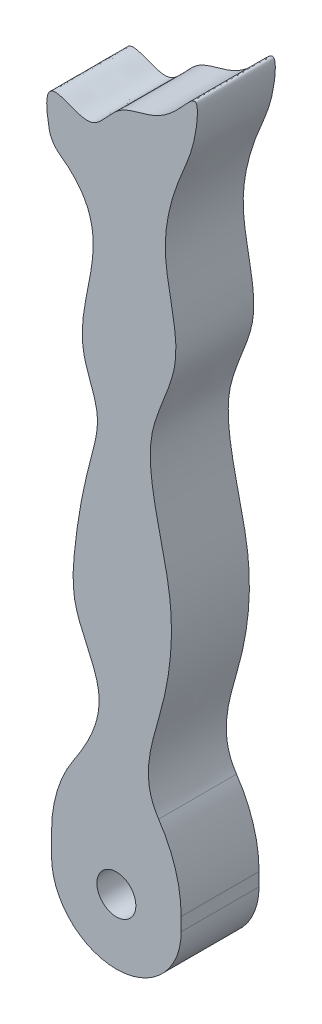
SolidWorks part; units mm, degrees
ref_plane "Front Plane" through (0, 0, 0) normal (0, 0, 1) x (1, 0, 0)
ref_plane "Top Plane" through (0, 0, 0) normal (0, 1, 0) x (1, 0, 0)
ref_plane "Right Plane" through (0, 0, 0) normal (1, 0, 0) x (0, 0, -1)
sketch "Sketch1" plane through (0, 0, 0) normal (0, 0, 1) x (1, 0, 0)
  line L0 (4.99, 0) -> (4.99, -9.98) construction
  line L1 (0, 0) -> (9.98, 0)
  line L2 (0, 0) -> (0, -9.98)
  line L3 (0, -9.98) -> (9.98, -9.98)
  line L4 (9.98, 0) -> (9.98, -9.98)
  line L5 (0, 0) -> (9.98, 0)
  circle A0 centre (4.99, -4.99) radius 1.5
  spline S0 degree 3 poles (0, 42.5974) (-1.3742, 48.5046) (2.7181, 43.5727) (4.8283, 47.7243) (7.8078, 48.1509) (9.4438, 49.2936) (11.3624, 51.6285) (11.1062, 47.8867) (9.7436, 45.2742) (7.96, 39.3631) (10.7082, 33.0622) (7.47, 28.047) (7.6846, 22.5231) (9.645, 16.8222) (8.8216, 8.4403) (6.0536, 2.653) (9.98, 0) knots 0 0 0 0 0.081694 0.122819 0.16076 0.205378 0.226065 0.252137 0.308778 0.39103 0.500424 0.587678 0.631959 0.740886 0.850026 1 1 1 1
  spline S1 degree 3 poles (0, 42.5974) (5.9992, 38.9776) (0.3774, 32.7882) (3.9926, 26.388) (2.5837, 21.7908) (1.7979, 17.4144) (1.4526, 12.0937) (5.426, 6.8361) (1.5097, 2.0179) (0, 0) knots 0 0 0 0 0.301225 0.380756 0.457987 0.608528 0.686338 0.807001 1 1 1 1
  dimension "D3" = 3
  dimension "D1" = 9.98
  dimension "D2" = 9.98
extrude "Boss-Extrude1" add sketch "Sketch1" along normal blind 6 contours S0 S1 L1 L5 | L5 L0 A0 L3 L4 | L0 L1 L2 L3 A0
fillet "Fillet1" radius 10 2 edges at (9.98, 0, 3) (0, 0, 3)
fillet "Fillet2" radius 2 1 edges at (0, 42.5974, 3)
fillet "Fillet3" radius 2 2 edges at (9.98, -9.98, 3) (0, -9.98, 3)
sketch "Sketch2" plane through (0, 0, 6) normal (0, 0, 1) x (1, 0, 0)
  line L1 (-2.5645, -4.99) -> (12.9111, -4.99)
  line L2 (-2.5645, -4.99) -> (-2.5645, -12.7018)
  line L3 (-2.5645, -12.7018) -> (12.9111, -12.7018)
  line L4 (12.9111, -4.99) -> (12.9111, -12.7018)
  circle A0 centre (4.99, -4.99) radius 4.99
  line M7 (2, -9.98) -> (7.98, -9.98)
  arc M8 (7.98, -9.98) -> (9.98, -7.98) centre (7.98, -7.98) ccw
  line M9 (9.98, -7.98) -> (9.98, -3.9703)
  line M15 (0, -3.2536) -> (0, -7.98)
  arc M16 (0, -7.98) -> (2, -9.98) centre (2, -7.98) ccw
extrude "Cut-Extrude1" cut sketch "Sketch2" against normal blind 10 contours A0 M15 M16 M7 | A0 M7 M8 M9
